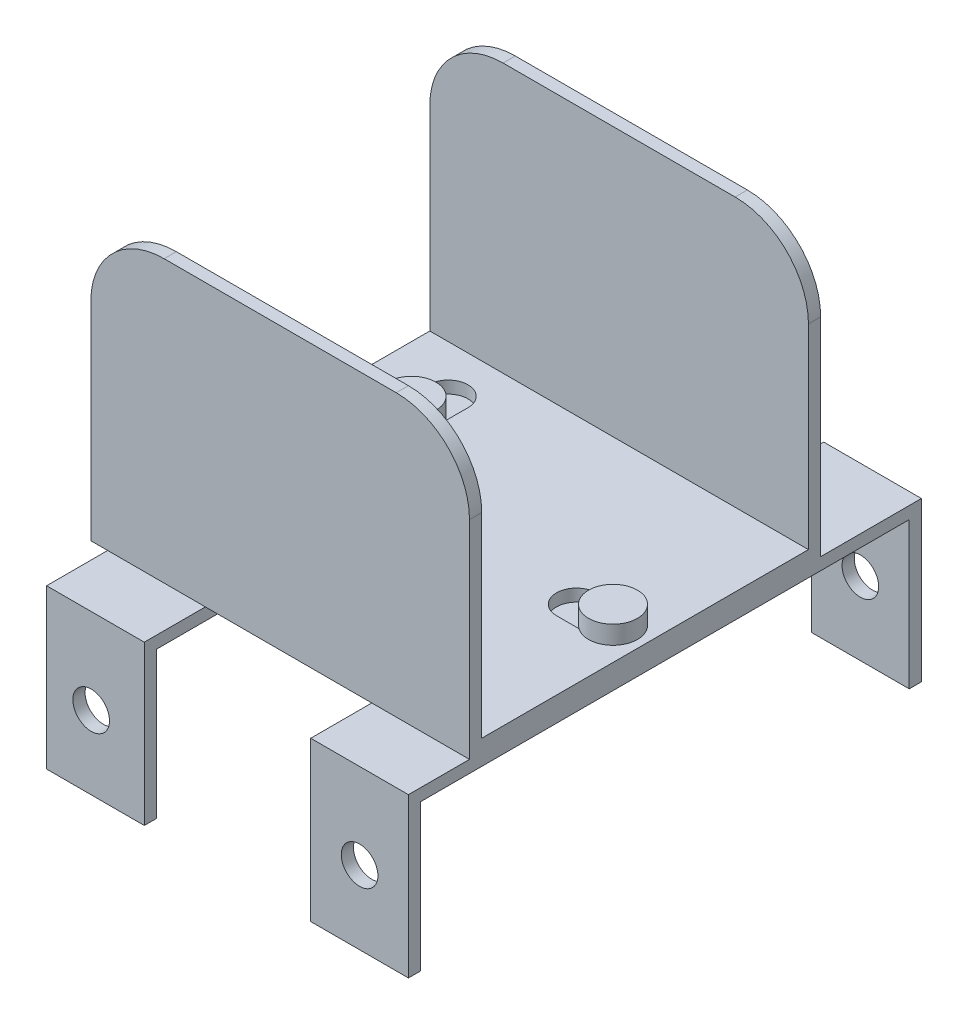
SolidWorks part; units mm, degrees
ref_plane "Front Plane" through (0, 0, 0) normal (0, 0, 1) x (1, 0, 0)
ref_plane "Top Plane" through (0, 0, 0) normal (0, 1, 0) x (1, 0, 0)
ref_plane "Right Plane" through (0, 0, 0) normal (1, 0, 0) x (0, 0, -1)
sketch "Sketch1" plane through (0, 0, 0) normal (0, 1, 0) x (1, 0, 0)
  line L0 (-25.4945, 45.6406) -> (136.9642, 45.6406) construction
  line L1 (0, 0) -> (98.425, 0)
  line L2 (0, 0) -> (0, 91.2812)
  line L3 (0, 91.2812) -> (98.425, 91.2812)
  line L4 (98.425, 0) -> (98.425, 91.2812)
  line L5 (17.0656, 112.0187) -> (17.0656, -29.9581) construction
  line L6 (9.8833, 25.0031) -> (25.2447, 25.0031) construction
  line L7 (9.8833, 66.2781) -> (25.2447, 66.2781) construction
  line L8 (17.0656, 66.2781) -> (17.0656, 75.8031) construction
  line L9 (11.9063, 66.2781) -> (11.9062, 75.8031)
  line L10 (22.225, 66.2781) -> (22.225, 75.8031)
  line L11 (17.0656, 25.0031) -> (17.0656, 15.4781) construction
  line L12 (11.9063, 25.0031) -> (11.9062, 15.4781)
  line L13 (22.225, 25.0031) -> (22.225, 15.4781)
  line L14 (80.5656, 61.557) -> (80.5656, 28.9632) construction
  line L15 (80.5656, 45.6406) -> (90.0906, 45.6406) construction
  line L16 (80.5656, 50.8) -> (90.0906, 50.8)
  line L17 (80.5656, 40.4812) -> (90.0906, 40.4812)
  arc A0 (11.9063, 66.2781) -> (22.225, 66.2781) centre (17.0656, 66.2781) ccw
  arc A1 (22.225, 75.8031) -> (11.9062, 75.8031) centre (17.0656, 75.8031) ccw
  arc A2 (11.9063, 25.0031) -> (22.225, 25.0031) centre (17.0656, 25.0031) cw
  arc A3 (22.225, 15.4781) -> (11.9062, 15.4781) centre (17.0656, 15.4781) cw
  circle A4 centre (17.0656, 45.6406) radius 5.1594
  arc A5 (80.5656, 50.8) -> (80.5656, 40.4812) centre (80.5656, 45.6406) ccw
  arc A6 (90.0906, 40.4812) -> (90.0906, 50.8) centre (90.0906, 45.6406) ccw
  point P15 (17.0656, 71.0406)
  point P22 (17.0656, 20.2406)
  point P31 (85.3281, 45.6406)
  dimension "D8" = 5.1594
  dimension "D9" = 63.5
  dimension "D11" = 5.1594
  dimension "D1" = 98.425
  dimension "D2" = 91.2812
  dimension "D3" = 17.0656
  dimension "D4" = 20.6375
  dimension "D5" = 20.6375
  dimension "D6" = 9.525
  dimension "D7" = 45.6406
  dimension "D10" = 9.525
extrude "Boss-Extrude1" add sketch "Sketch1" along normal blind 3.175
sketch "Sketch2" plane through (0, 0, 0) normal (0, -1, 0) x (1, 0, 0)
  line L0 (-23.3612, -25.4) -> (145.6802, -25.4) construction
  line L1 (-23.3612, -76.2) -> (148.0951, -76.2) construction
  line L2 (0, 0) -> (98.425, 0) construction
  line L3 (98.425, 0) -> (98.425, -91.2812) construction
  line L14 (4.3656, 15.875) -> (29.7656, 15.875)
  line L15 (4.3656, 15.875) -> (4.3656, -117.475)
  line L16 (4.3656, -117.475) -> (29.7656, -117.475)
  line L17 (29.7656, 15.875) -> (29.7656, -117.475)
  line L18 (98.425, 15.875) -> (73.025, 15.875)
  line L19 (98.425, 15.875) -> (98.425, -117.475)
  line L20 (98.425, -117.475) -> (73.025, -117.475)
  line L21 (73.025, 15.875) -> (73.025, -117.475)
  circle A0 centre (17.0656, -45.6406) radius 5.1594 construction
  dimension "D1" = 50.8
  dimension "D2" = 25.4
  dimension "D3" = 41.275
  dimension "D4" = 41.275
  dimension "D5" = 41.275
  dimension "D6" = 41.275
  dimension "D7" = 25.4
  dimension "D8" = 25.4
  dimension "D9" = 0
  dimension "D10" = 12.7
extrude "Boss-Extrude3" add sketch "Sketch2" along normal blind 3.175
sketch "Sketch3" plane through (0, -3.175, 0) normal (0, -1, 0) x (1, 0, 0)
  line L0 (29.7656, -117.475) -> (29.7656, 15.875) construction
  line L1 (4.3656, 15.875) -> (29.7656, 15.875)
  line L3 (4.3656, 12.7) -> (29.7656, 12.7)
  line L4 (29.7656, 15.875) -> (29.7656, 12.7)
  line L5 (4.3656, 15.875) -> (4.3656, -117.475) construction
  line L6 (4.3656, -114.3) -> (29.7656, -114.3)
  line L7 (4.3656, -114.3) -> (4.3656, -117.475)
  line L8 (4.3656, -117.475) -> (29.7656, -117.475)
  line L9 (29.7656, -114.3) -> (29.7656, -117.475)
  line L10 (98.425, -117.475) -> (98.425, 15.875) construction
  line L11 (73.025, 15.875) -> (98.425, 15.875)
  line L12 (73.025, 15.875) -> (73.025, 12.7)
  line L13 (73.025, 12.7) -> (98.425, 12.7)
  line L14 (98.425, 15.875) -> (98.425, 12.7)
  line L15 (4.3656, 15.875) -> (4.3656, 12.7)
  line L16 (73.025, -117.475) -> (98.425, -117.475)
  line L17 (73.025, -117.475) -> (73.025, -114.3)
  line L18 (73.025, -114.3) -> (98.425, -114.3)
  line L19 (98.425, -117.475) -> (98.425, -114.3)
  dimension "D1" = 3.175
  dimension "D2" = 3.175
  dimension "D3" = 3.175
  dimension "D4" = 3.175
extrude "Boss-Extrude4" add sketch "Sketch3" along normal blind 38.1
sketch "Sketch4" plane through (0, 0, 15.875) normal (0, 0, 1) x (1, 0, 0)
  line L0 (-6.3689, -22.225) -> (106.2336, -22.225) construction
  line L1 (15.9599, -1.7661) -> (15.9599, -48.5144) construction
  line L2 (85.725, 0) -> (85.725, -43.096) construction
  line L3 (73.025, 0) -> (98.425, 0) construction
  line L5 (98.425, -41.275) -> (73.025, -41.275) construction
  circle A0 centre (15.9599, -22.225) radius 4.7625
  circle A1 centre (85.725, -22.225) radius 4.7625
  dimension "D1" = 19.05
  dimension "D2" = 9.525
  dimension "D3" = 9.525
extrude "Cut-Extrude1" cut sketch "Sketch4" against normal through all
sketch "Sketch5" plane through (0, 3.175, 0) normal (0, 1, 0) x (1, 0, 0)
  circle A0 centre (17.0656, 45.6406) radius 5.1594
  circle A1 centre (17.0656, 66.2781) radius 5.1594
  circle A2 centre (90.0906, 45.6406) radius 5.1594
extrude "Boss-Extrude5" add sketch "Sketch5" against normal blind 9.525
sketch "Sketch6" plane through (0, 3.175, 0) normal (0, 1, 0) x (1, 0, 0)
  circle A1 centre (90.0906, 45.6406) radius 6.35
  circle A2 centre (17.0656, 45.6406) radius 6.35
  circle A3 centre (17.0656, 66.2781) radius 6.35
extrude "Boss-Extrude6" add sketch "Sketch6" along normal blind 4.7625
sketch "Sketch7" plane through (0, 3.175, 0) normal (0, 1, 0) x (1, 0, 0)
  line L5 (98.425, 0) -> (98.425, 91.2812) construction
  line L10 (0, 91.2812) -> (98.425, 91.2812)
  line L11 (0, 91.2812) -> (0, 88.1063)
  line L12 (0, 88.1063) -> (98.425, 88.1063)
  line L13 (98.425, 91.2812) -> (98.425, 88.1063)
  line L14 (0, 91.2812) -> (0, 0) construction
  line L15 (0, 3.175) -> (98.425, 3.175)
  line L16 (0, 3.175) -> (0, 0)
  line L17 (0, 0) -> (98.425, 0)
  line L18 (98.425, 3.175) -> (98.425, 0)
  dimension "D1" = 3.175
  dimension "D2" = 3.175
extrude "Boss-Extrude7" add sketch "Sketch7" along normal blind 69.85
sketch "Sketch8" plane through (0, 0, 0) normal (0, 0, 1) x (1, 0, 0)
  line L2 (79.375, 81.5411) -> (79.375, 48.9) construction
  line L3 (109.6686, 53.975) -> (75.6312, 53.975) construction
  line L4 (19.05, 81.5411) -> (19.05, 46.8054) construction
  line L5 (-18.9754, 53.975) -> (30.4225, 53.975) construction
  line L6 (0, 73.025) -> (0, 0) construction
  line L8 (0, 73.025) -> (98.425, 73.025) construction
  line L9 (98.425, 73.025) -> (98.425, 0) construction
  line L10 (79.375, 73.025) -> (98.425, 73.025)
  line L11 (98.425, 73.025) -> (98.425, 53.975)
  line L12 (19.05, 73.025) -> (0, 73.025)
  line L13 (0, 73.025) -> (0, 53.975)
  arc A0 (79.375, 73.025) -> (98.425, 53.975) centre (79.375, 53.975) cw
  arc A1 (19.05, 73.025) -> (0, 53.975) centre (19.05, 53.975) ccw
  dimension "D2" = 19.05
  dimension "D1" = 19.05
  dimension "D3" = 19.05
extrude "Cut-Extrude2" cut sketch "Sketch8" against normal through all both and the other way through all
